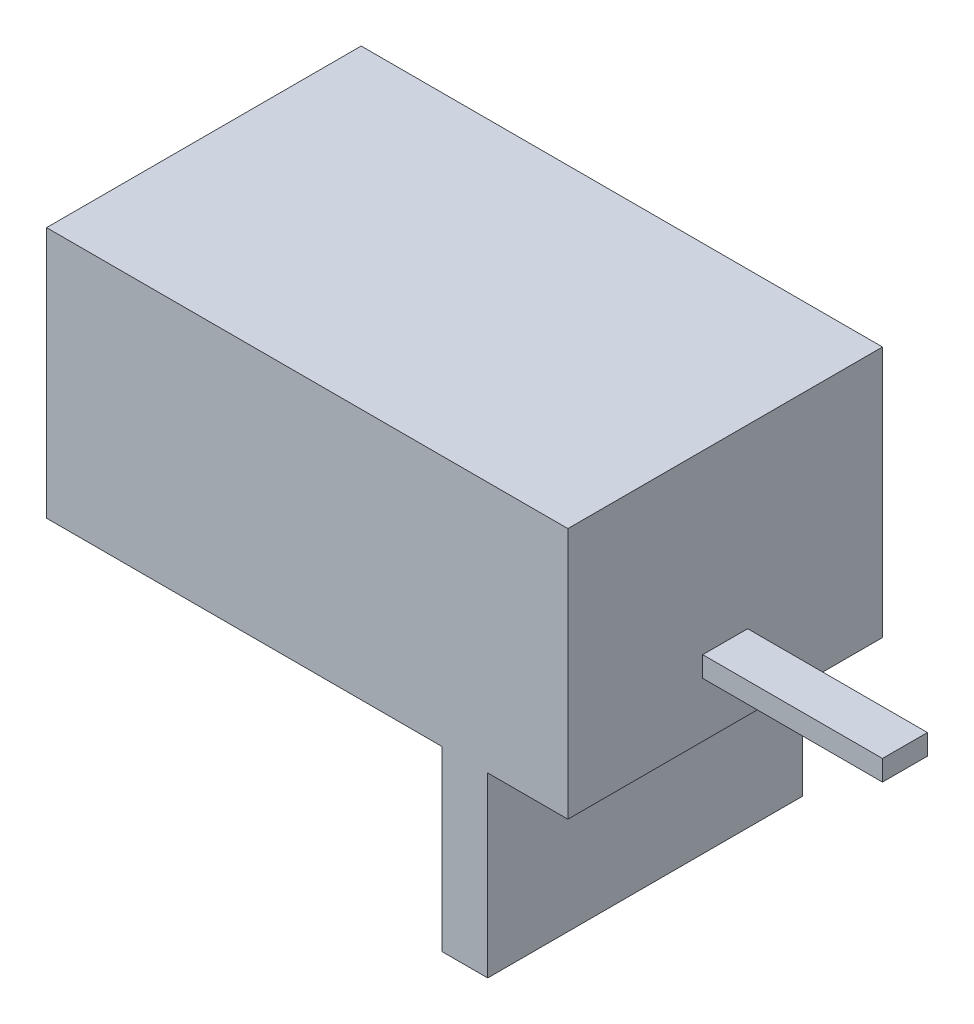
SolidWorks part; units mm, degrees
ref_plane "Front Plane" through (0, 0, 0) normal (0, 0, 1) x (1, 0, 0)
ref_plane "Top Plane" through (0, 0, 0) normal (0, 1, 0) x (1, 0, 0)
ref_plane "Right Plane" through (0, 0, 0) normal (1, 0, 0) x (0, 0, -1)
sketch "Sketch1" plane through (0, 0, 0) normal (0, 1, 0) x (1, 0, 0)
  line L1 (-145, -87.5) -> (145, -87.5)
  line L2 (-145, -87.5) -> (-145, 87.5)
  line L3 (-145, 87.5) -> (145, 87.5)
  line L4 (145, -87.5) -> (145, 87.5)
  line L5 (-145, -87.5) -> (145, 87.5) construction
  line L6 (-145, 87.5) -> (145, -87.5) construction
  point P0 (0, 0)
  dimension "D1" = 290
  dimension "D2" = 175
extrude "Boss-Extrude1" add sketch "Sketch1" along normal blind 140
sketch "Sketch2" plane through (0, 0, 0) normal (0, -1, 0) x (1, 0, 0)
  line L0 (145, -87.5) -> (-145, -87.5) construction
  line L1 (75, 87.5) -> (100.4, 87.5)
  line L3 (75, -87.5) -> (100.4, -87.5)
  line L4 (100.4, 87.5) -> (100.4, -87.5)
  line L6 (75, 87.5) -> (75, -87.5)
  line L7 (-145, 87.5) -> (145, 87.5) construction
  line L8 (-145, -87.5) -> (-145, 87.5) construction
  dimension "D1" = 220
  dimension "D2" = 25.4
extrude "Boss-Extrude2" add sketch "Sketch2" along normal blind 98.8 contours L1 L4 L3 L6
sketch "Sketch3" plane through (145, 0, 0) normal (1, 0, 0) x (0, 0, -1)
  line L1 (-12.5, 41.7643) -> (12.5, 41.7643)
  line L3 (-12.5, 30.3682) -> (12.5, 30.3682)
  line L6 (-87.5, 140) -> (-87.5, 0) construction
  line L7 (-12.5, 41.7643) -> (12.5, 41.7643)
  line L8 (-12.5, 41.7643) -> (-12.5, 30.3682)
  line L9 (-12.5, 30.3682) -> (12.5, 30.3682)
  line L10 (12.5, 41.7643) -> (12.5, 30.3682)
  line L11 (87.5, 140) -> (87.5, 0) construction
  dimension "D1" = 75
  dimension "D2" = 75
extrude "Boss-Extrude3" add sketch "Sketch3" along normal blind 100 contours L10 L1 L8 L3
